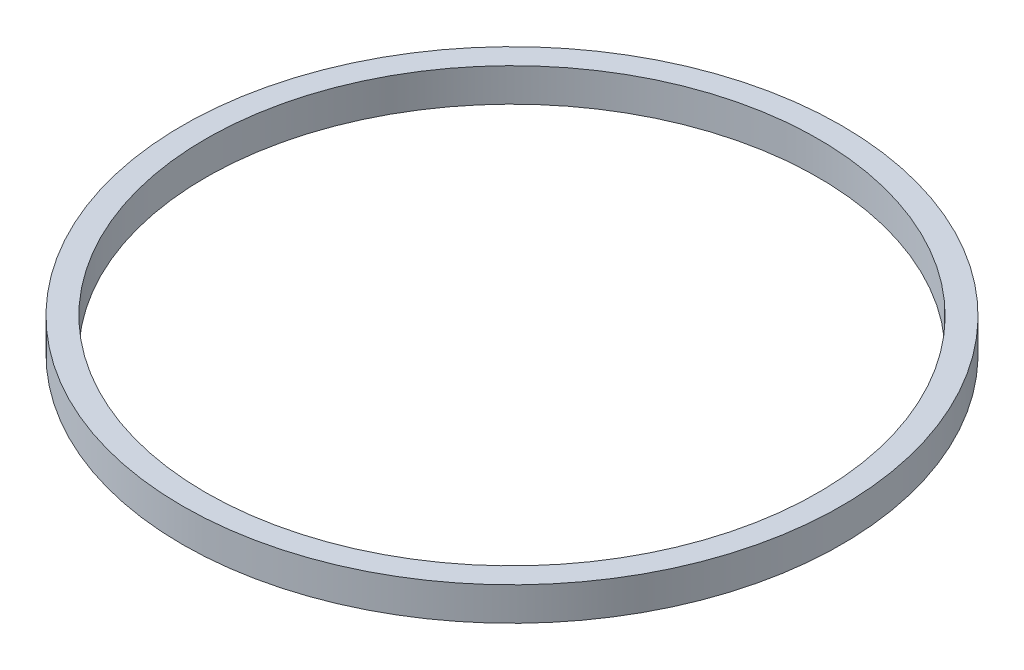
SolidWorks part; units mm, degrees
ref_plane "Front Plane" through (0, 0, 0) normal (0, 0, 1) x (1, 0, 0)
ref_plane "Top Plane" through (0, 0, 0) normal (0, 1, 0) x (1, 0, 0)
ref_plane "Right Plane" through (0, 0, 0) normal (1, 0, 0) x (0, 0, -1)
sketch "Sketch1" plane through (0, 0, 0) normal (0, 1, 0) x (1, 0, 0)
  circle A0 centre (0, 0) radius 1003.3
  circle A1 centre (0, 0) radius 1079.5
  dimension "D1" = 2006.6
  dimension "D2" = 2159
extrude "Boss-Extrude1" add sketch "Sketch1" along normal blind 109.22
